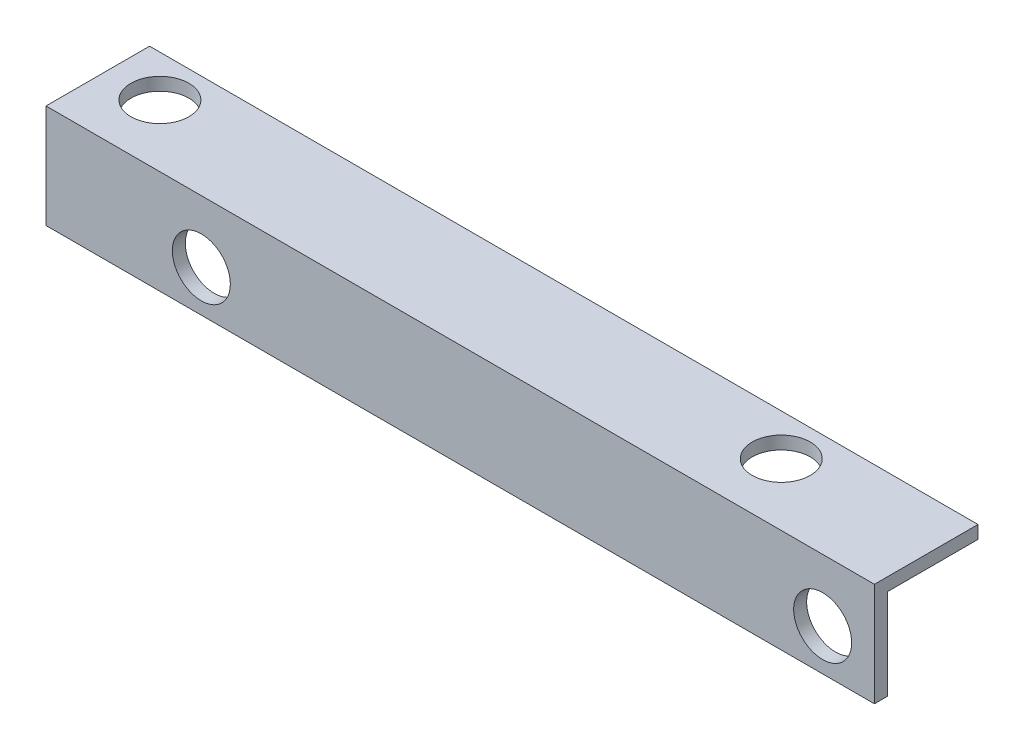
SolidWorks part; units mm, degrees
material "5052-H32"
ref_plane "Front Plane" through (0, 0, 0) normal (0, 0, 1) x (1, 0, 0)
ref_plane "Top Plane" through (0, 0, 0) normal (0, 1, 0) x (1, 0, 0)
ref_plane "Right Plane" through (0, 0, 0) normal (1, 0, 0) x (0, 0, -1)
sketch "Sketch1" plane through (0, 0, 0) normal (1, 0, 0) x (0, 0, -1)
  line L0 (0, 0) -> (0, 12.7)
  line L1 (0, 55) -> (0, -55) construction
  line L2 (0, 12.7) -> (12.7, 12.7)
  line L3 (1.5875, 0) -> (1.5875, 11.1125)
  line L4 (1.5875, 11.1125) -> (12.7, 11.1125)
  line L5 (12.7, 12.7) -> (12.7, 11.1125)
  line L6 (0, 0) -> (1.5875, 0)
  dimension "D1" = 12.7
  dimension "D2" = 12.7
  dimension "D3" = 1.5875
extrude "Boss-Extrude1" add sketch "Sketch1" along normal blind 44.45 and the other way blind 57.15
sketch "Sketch3" plane through (0, 0, 0) normal (0, 0, 1) x (1, 0, 0)
  line L0 (-57.15, 12.7) -> (44.45, 12.7) construction
  line L1 (44.45, 12.7) -> (44.45, 0) construction
  line L2 (-38.1, 5.08) -> (38.1, 5.08) construction
  circle A0 centre (-38.1, 5.08) radius 3.556
  circle A1 centre (38.1, 5.08) radius 3.556
  dimension "D1" = 7.112
  dimension "D2" = 7.62
  dimension "D3" = 76.2
  dimension "D4" = 6.35
extrude "Cut-Extrude1" cut sketch "Sketch3" against normal through all
sketch "Sketch5" plane through (0, 12.7, 0) normal (0, 1, 0) x (1, 0, 0)
  line L0 (-50.8, 7.62) -> (25.4, 7.62) construction
  line L1 (-6.985, 0) -> (6.985, 0) construction
  line L2 (-57.15, 12.7) -> (-57.15, 0) construction
  circle A0 centre (-50.8, 7.62) radius 3.556
  circle A1 centre (25.4, 7.62) radius 3.556
  point P6 (29.9141, 7.62)
  dimension "D1" = 7.112
  dimension "D4" = 6.35
  dimension "D2" = 7.62
  dimension "D3" = 76.2
extrude "Cut-Extrude2" cut sketch "Sketch5" against normal through all
